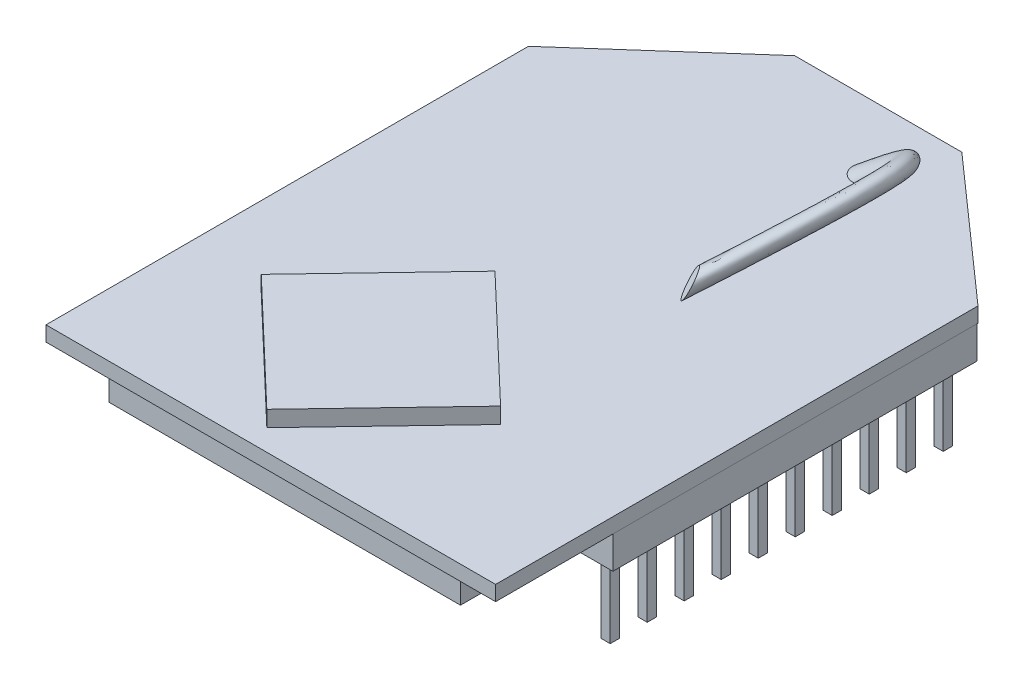
SolidWorks part; units mm, degrees
ref_plane "Front Plane" through (0, 0, 0) normal (0, 0, 1) x (1, 0, 0)
ref_plane "Top Plane" through (0, 0, 0) normal (0, 1, 0) x (1, 0, 0)
ref_plane "Right Plane" through (0, 0, 0) normal (1, 0, 0) x (0, 0, -1)
sketch "Sketch1" plane through (0, 0, 0) normal (0, 1, 0) x (1, 0, 0)
  line L0 (0, 0) -> (24.384, 0)
  line L1 (24.384, 0) -> (24.384, 26.162)
  line L2 (24.384, 26.162) -> (16.7259, 32.9438)
  line L3 (16.7259, 32.9438) -> (7.6581, 32.9438)
  line L4 (7.6581, 32.9438) -> (0, 26.162)
  line L5 (0, 26.162) -> (0, 0)
  dimension "D1" = 24.384
  dimension "D2" = 32.9438
  dimension "D3" = 26.162
  dimension "D4" = 9.0678
extrude "Boss-Extrude1" add sketch "Sketch1" along normal blind 0.8128
sketch "Sketch2" plane through (0, 0, 0) normal (0, -1, 0) x (-1, 0, 0)
  line L0 (0, 0) -> (-24.384, 0) construction
  line L1 (-2.667, 0.762) -> (-21.717, 0.762)
  line L2 (-2.667, 0.762) -> (-2.667, 24.9682)
  line L3 (-2.667, 24.9682) -> (-21.717, 24.9682)
  line L4 (-21.717, 0.762) -> (-21.717, 24.9682)
  line L5 (-12.192, 32.9438) -> (-12.192, -21.3994) construction
  line L6 (-16.7259, 32.9438) -> (-7.6581, 32.9438) construction
  point P10 (-12.192, 24.9682)
  dimension "D1" = 19.05
  dimension "D2" = 24.2062
  dimension "D3" = 0.762
extrude "Boss-Extrude2" add sketch "Sketch2" along normal blind 1.8796
sketch "Sketch3" plane through (0, 0.8128, 0) normal (0, 1, 0) x (1, 0, 0)
  line L0 (4.3307, 7.3425) -> (10.5175, 13.8322)
  line L1 (10.5175, 13.8322) -> (17.0072, 7.6454)
  line L2 (17.0072, 7.6454) -> (10.8204, 1.1557)
  line L3 (10.8204, 1.1557) -> (4.3307, 7.3425)
  line L4 (24.384, 0) -> (24.384, 26.162) construction
  line L5 (16.7259, 32.9438) -> (7.6581, 32.9438) construction
  dimension "D1" = 8.9662
  dimension "D2" = 20.0533
  dimension "D3" = 31.7881
  dimension "D4" = 13.5636
extrude "Boss-Extrude3" add sketch "Sketch3" along normal blind 0.8636
sketch "Sketch4" plane through (0, 0, 0) normal (0, -1, 0) x (-1, 0, 0)
  line L0 (-2.0066, 26.1366) -> (-2.0066, 6.3866)
  line L1 (-24.3586, 26.1366) -> (-22.3774, 26.1366)
  line L2 (-24.3586, 26.1366) -> (-24.3586, 6.3866)
  line L3 (-24.3586, 6.3866) -> (-22.3774, 6.3866)
  line L4 (-22.3774, 26.1366) -> (-22.3774, 6.3866)
  line L5 (-12.192, 0) -> (-12.192, 34.9186) construction
  line L6 (-24.384, 0) -> (-24.384, 26.162) construction
  line L7 (0, 0) -> (-24.384, 0) construction
  line L8 (-0.0254, 6.3866) -> (-2.0066, 6.3866)
  line L9 (-0.0254, 26.1366) -> (-0.0254, 6.3866)
  line L10 (-0.0254, 26.1366) -> (-2.0066, 26.1366)
  dimension "D1" = 1.9812
  dimension "D2" = 19.75
  dimension "D3" = 0.0254
  dimension "D4" = 0.0254
extrude "Boss-Extrude4" add sketch "Sketch4" along normal blind 1.778
sketch "Sketch5" plane through (0, -1.778, 0) normal (0, -1, 0) x (-1, 0, 0)
  line L0 (-23.368, 6.3866) -> (-23.368, 26.1366) construction
  line L1 (-23.114, 25.5453) -> (-23.622, 25.5453)
  line L2 (-23.114, 25.5453) -> (-23.114, 25.0373)
  line L3 (-23.114, 25.0373) -> (-23.622, 25.0373)
  line L4 (-23.622, 25.5453) -> (-23.622, 25.0373)
  line L5 (-24.3586, 6.3866) -> (-22.3774, 6.3866) construction
  line L6 (-22.3774, 26.1366) -> (-24.3586, 26.1366) construction
  line L7 (-12.192, 0) -> (-12.192, 32.9438) construction
  line L8 (-23.622, 23.5387) -> (-23.622, 23.0307)
  line L9 (-23.114, 23.5387) -> (-23.622, 23.5387)
  line L10 (-23.114, 23.0307) -> (-23.622, 23.0307)
  line L11 (-23.114, 23.5387) -> (-23.114, 23.0307)
  line L12 (-23.622, 21.5321) -> (-23.622, 21.0241)
  line L13 (-23.114, 21.5321) -> (-23.622, 21.5321)
  line L14 (-23.114, 21.0241) -> (-23.622, 21.0241)
  line L15 (-23.114, 21.5321) -> (-23.114, 21.0241)
  line L16 (-23.622, 19.5255) -> (-23.622, 19.0175)
  line L17 (-23.114, 19.5255) -> (-23.622, 19.5255)
  line L18 (-23.114, 19.0175) -> (-23.622, 19.0175)
  line L19 (-23.114, 19.5255) -> (-23.114, 19.0175)
  line L20 (-23.622, 17.5189) -> (-23.622, 17.0109)
  line L21 (-23.114, 17.5189) -> (-23.622, 17.5189)
  line L22 (-23.114, 17.0109) -> (-23.622, 17.0109)
  line L23 (-23.114, 17.5189) -> (-23.114, 17.0109)
  line L24 (-23.622, 15.5123) -> (-23.622, 15.0043)
  line L25 (-23.114, 15.5123) -> (-23.622, 15.5123)
  line L26 (-23.114, 15.0043) -> (-23.622, 15.0043)
  line L27 (-23.114, 15.5123) -> (-23.114, 15.0043)
  line L28 (-23.622, 13.5057) -> (-23.622, 12.9977)
  line L29 (-23.114, 13.5057) -> (-23.622, 13.5057)
  line L30 (-23.114, 12.9977) -> (-23.622, 12.9977)
  line L31 (-23.114, 13.5057) -> (-23.114, 12.9977)
  line L32 (-23.622, 11.4991) -> (-23.622, 10.9911)
  line L33 (-23.114, 11.4991) -> (-23.622, 11.4991)
  line L34 (-23.114, 10.9911) -> (-23.622, 10.9911)
  line L35 (-23.114, 11.4991) -> (-23.114, 10.9911)
  line L36 (-23.622, 9.4925) -> (-23.622, 8.9845)
  line L37 (-23.114, 9.4925) -> (-23.622, 9.4925)
  line L38 (-23.114, 8.9845) -> (-23.622, 8.9845)
  line L39 (-23.114, 9.4925) -> (-23.114, 8.9845)
  line L40 (-23.622, 7.4859) -> (-23.622, 6.9779)
  line L41 (-23.114, 7.4859) -> (-23.622, 7.4859)
  line L42 (-23.114, 6.9779) -> (-23.622, 6.9779)
  line L43 (-23.114, 7.4859) -> (-23.114, 6.9779)
  line L44 (-23.5316, 25.5453) -> (-23.5316, 26.1366) construction
  line L45 (-23.5316, 6.9779) -> (-23.5316, 6.3866) construction
  line L46 (-24.3586, 6.3866) -> (-22.3774, 6.3866) construction
  line L47 (0, 0) -> (-24.384, 0) construction
  line L48 (-16.7259, 32.9438) -> (-7.6581, 32.9438) construction
  line L49 (-0.8524, 6.9779) -> (-0.8524, 6.3866) construction
  line L50 (-0.8524, 25.5453) -> (-0.8524, 26.1366) construction
  line L51 (-1.016, 6.3866) -> (-1.016, 26.1366) construction
  line L52 (-1.27, 7.4859) -> (-1.27, 6.9779)
  line L53 (-1.27, 6.9779) -> (-0.762, 6.9779)
  line L54 (-1.27, 7.4859) -> (-0.762, 7.4859)
  line L55 (-0.762, 7.4859) -> (-0.762, 6.9779)
  line L56 (-1.27, 9.4925) -> (-1.27, 8.9845)
  line L57 (-1.27, 8.9845) -> (-0.762, 8.9845)
  line L58 (-1.27, 9.4925) -> (-0.762, 9.4925)
  line L59 (-0.762, 9.4925) -> (-0.762, 8.9845)
  line L60 (-1.27, 11.4991) -> (-1.27, 10.9911)
  line L61 (-1.27, 10.9911) -> (-0.762, 10.9911)
  line L62 (-1.27, 11.4991) -> (-0.762, 11.4991)
  line L63 (-0.762, 11.4991) -> (-0.762, 10.9911)
  line L64 (-1.27, 13.5057) -> (-1.27, 12.9977)
  line L65 (-1.27, 12.9977) -> (-0.762, 12.9977)
  line L66 (-1.27, 13.5057) -> (-0.762, 13.5057)
  line L67 (-0.762, 13.5057) -> (-0.762, 12.9977)
  line L68 (-1.27, 15.5123) -> (-1.27, 15.0043)
  line L69 (-1.27, 15.0043) -> (-0.762, 15.0043)
  line L70 (-1.27, 15.5123) -> (-0.762, 15.5123)
  line L71 (-0.762, 15.5123) -> (-0.762, 15.0043)
  line L72 (-1.27, 17.5189) -> (-1.27, 17.0109)
  line L73 (-1.27, 17.0109) -> (-0.762, 17.0109)
  line L74 (-1.27, 17.5189) -> (-0.762, 17.5189)
  line L75 (-0.762, 17.5189) -> (-0.762, 17.0109)
  line L76 (-1.27, 19.5255) -> (-1.27, 19.0175)
  line L77 (-1.27, 19.0175) -> (-0.762, 19.0175)
  line L78 (-1.27, 19.5255) -> (-0.762, 19.5255)
  line L79 (-0.762, 19.5255) -> (-0.762, 19.0175)
  line L80 (-1.27, 21.5321) -> (-1.27, 21.0241)
  line L81 (-1.27, 21.0241) -> (-0.762, 21.0241)
  line L82 (-1.27, 21.5321) -> (-0.762, 21.5321)
  line L83 (-0.762, 21.5321) -> (-0.762, 21.0241)
  line L84 (-1.27, 23.5387) -> (-1.27, 23.0307)
  line L85 (-1.27, 23.0307) -> (-0.762, 23.0307)
  line L86 (-1.27, 23.5387) -> (-0.762, 23.5387)
  line L87 (-0.762, 23.5387) -> (-0.762, 23.0307)
  line L88 (-0.762, 25.5453) -> (-0.762, 25.0373)
  line L89 (-1.27, 25.0373) -> (-0.762, 25.0373)
  line L90 (-1.27, 25.5453) -> (-1.27, 25.0373)
  line L91 (-1.27, 25.5453) -> (-0.762, 25.5453)
  point P10 (-23.368, 25.5453)
  point P53 (-23.368, 6.9779)
  point P106 (-1.016, 6.9779)
  point P107 (-1.016, 25.5453)
  dimension "D1" = 0.508
  dimension "D2" = 2.0066
  dimension "D3" = 10
extrude "Boss-Extrude5" add sketch "Sketch5" along normal blind 4.064
sketch "Sketch6" plane through (0, 0.8128, 0) normal (0, 1, 0) x (1, 0, 0)
  line L0 (15.1892, 30.099) -> (8.0952, 30.099) construction
  line L1 (15.9512, 29.337) -> (15.9512, 23.2643) construction
  line L2 (0, 26.162) -> (0, 0) construction
  line L3 (0, 0) -> (24.384, 0) construction
  circle A0 centre (15.1892, 29.337) radius 0.762
  dimension "D1" = 1.524
  dimension "D2" = 15.9512
  dimension "D3" = 30.099
sketch3d "3DSketch1"
  spline S0 degree 2 poles (15.1892, 0.8128, -29.337) (20.623, 5, -30.4486) (16.9898, 2.292, -17.9512) knots 0 0 0 1 1 1
sweep "Sweep2" add profiles "Sketch6" path "3DSketch1"
